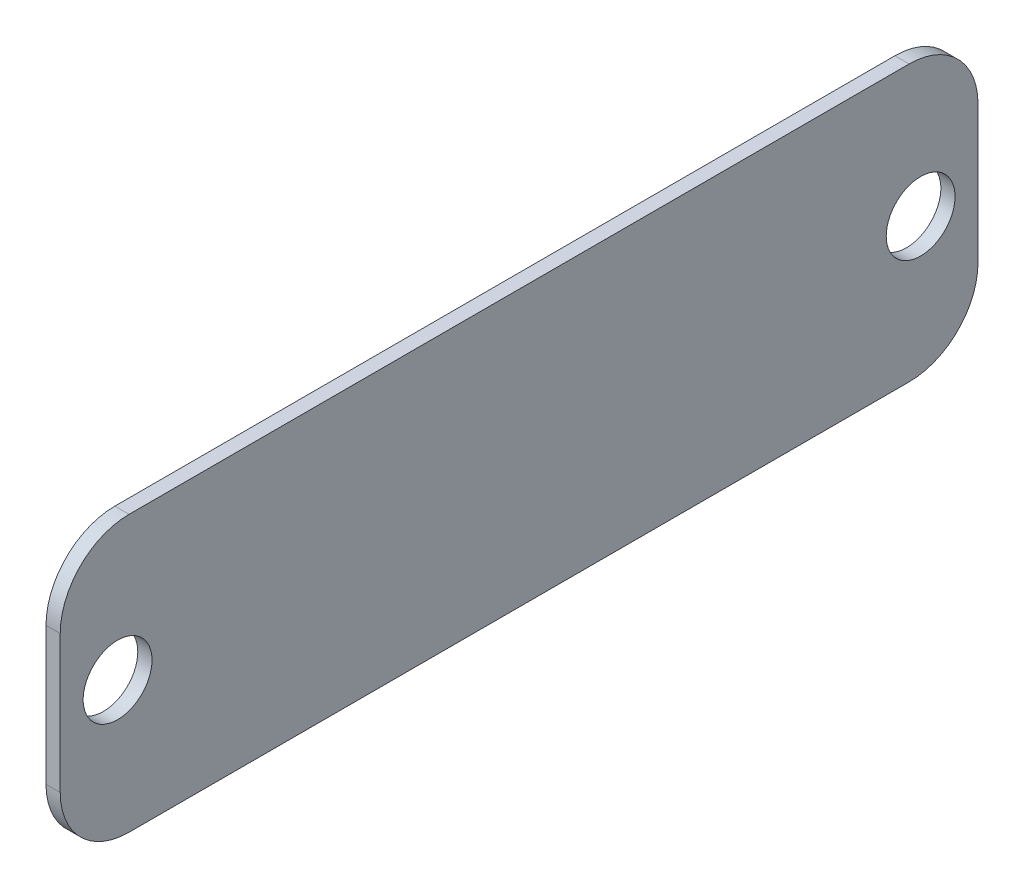
SolidWorks part; units mm, degrees
ref_plane "Alzado" through (0, 0, 0) normal (0, 0, 1) x (1, 0, 0)
ref_plane "Planta" through (0, 0, 0) normal (0, 1, 0) x (1, 0, 0)
ref_plane "Vista lateral" through (0, 0, 0) normal (1, 0, 0) x (0, 0, -1)
sketch "Croquis1" plane through (0, 0, 0) normal (1, 0, 0) x (0, 0, -1)
  line L1 (-100, -30) -> (100, -30)
  line L2 (-100, -30) -> (-100, 30)
  line L3 (-100, 30) -> (100, 30)
  line L4 (100, -30) -> (100, 30)
  line L5 (-100, -30) -> (100, 30) construction
  line L6 (-100, 30) -> (100, -30) construction
  point P0 (0, 0)
  dimension "D1" = 200
  dimension "D2" = 60
extrude "Saliente-Extruir1" add sketch "Croquis1" along normal mid plane 3.1
fillet "Redondeo1" radius 15 4 edges at (0, -30, -100) (0, 30, -100) (0, -30, 100) (0, 30, 100)
sketch "Croquis2" plane through (1.55, 0, 0) normal (1, 0, 0) x (0, 0, -1)
  line L0 (0, 0) -> (-84.6078, 0) construction
  line L1 (0, 0) -> (0, 18.3275) construction
  line L2 (-100, 15) -> (-100, -15) construction
  circle A0 centre (-87.5, 0) radius 7.5
  circle A1 centre (87.5, 0) radius 7.5
  dimension "D1" = 15
  dimension "D2" = 12.5
extrude "Cortar-Extruir1" cut sketch "Croquis2" against normal up to surface (3.1 mm away) up to face at (-1.55, 0, 0)
